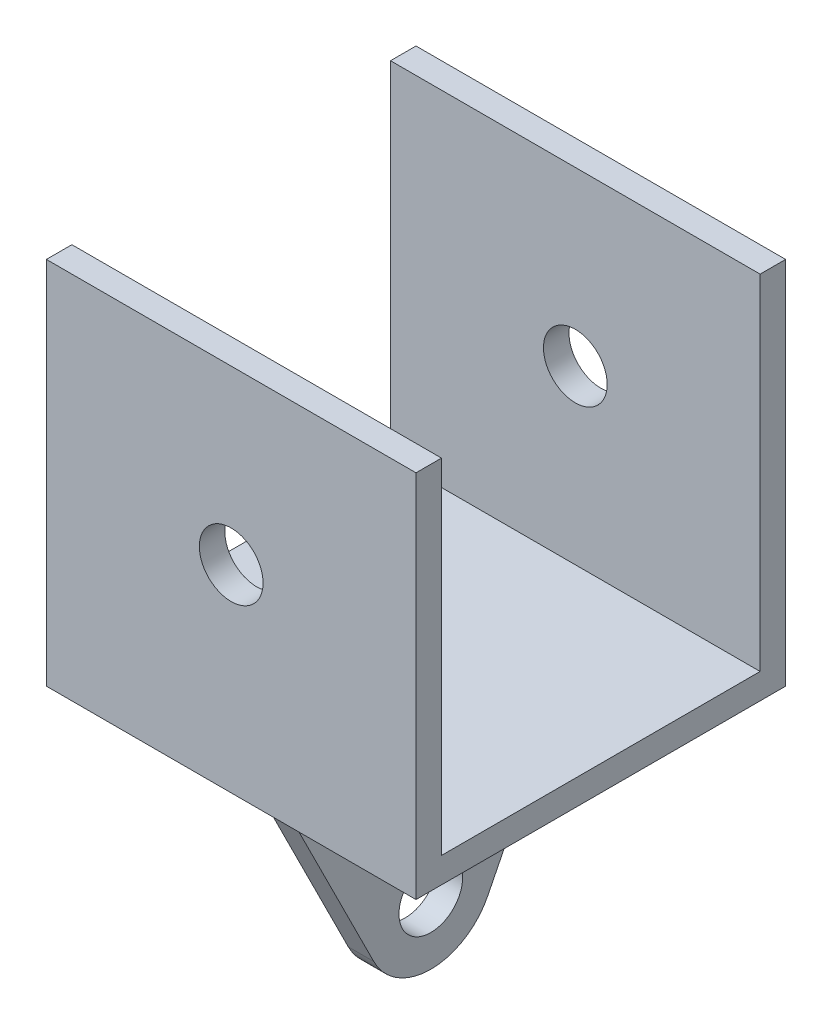
SolidWorks part; units mm, degrees
ref_plane "Front Plane" through (0, 0, 0) normal (0, 0, 1) x (1, 0, 0)
ref_plane "Top Plane" through (0, 0, 0) normal (0, 1, 0) x (1, 0, 0)
ref_plane "Right Plane" through (0, 0, 0) normal (1, 0, 0) x (0, 0, -1)
sketch "Sketch1" plane through (0, 0, 0) normal (0, 1, 0) x (1, 0, 0)
  line L0 (-14.5, 14.5) -> (14.5, -14.5) construction
  line L1 (-14.5, 14.5) -> (14.5, 14.5)
  line L2 (-14.5, 14.5) -> (-14.5, -14.5)
  line L3 (-14.5, -14.5) -> (14.5, -14.5)
  line L4 (14.5, 14.5) -> (14.5, -14.5)
extrude "Boss-Extrude1" add sketch "Sketch1" along normal blind 2
sketch "Sketch2" plane through (0, 2, 0) normal (0, 1, 0) x (1, 0, 0)
  line L0 (14.5, -14.5) -> (14.5, 14.5) construction
  line L1 (-14.5, -14.5) -> (14.5, -14.5)
  line L2 (-14.5, -14.5) -> (-14.5, -12.5)
  line L3 (-14.5, -12.5) -> (14.5, -12.5)
  line L4 (14.5, -14.5) -> (14.5, -12.5)
  dimension "D1" = 2
extrude "Boss-Extrude2" add sketch "Sketch2" along normal blind 27
mirror "Mirror1" about plane through (0, 0, 0) normal (0, 0, 1) of "Boss-Extrude2"
sketch "Sketch4" plane through (0, 0, 14.5) normal (0, 0, 1) x (1, 0, 0)
  line L0 (-14.5, 29) -> (14.5, 2) construction
  line L1 (14.5, 29) -> (14.5, 0) construction
  line L2 (-14.5, 0) -> (14.5, 0) construction
  line L3 (-14.5, 2) -> (14.5, 29) construction
  circle A0 centre (0, 15.5) radius 2.5
  dimension "D1" = 2
extrude "Cut-Extrude1" cut sketch "Sketch4" against normal through all
sketch "Sketch6" plane through (0, 0, 0) normal (1, 0, 0) x (0, 0, -1)
  line L0 (-12.3405, 0) -> (12.6624, 0)
  line L1 (-14.5, 0) -> (14.5, 0) construction
  line L2 (12.6624, 0) -> (4.633, -16.057)
  line L3 (-4.3111, -16.057) -> (-12.3405, 0)
  arc A0 (4.633, -16.057) -> (-4.3111, -16.057) centre (0.161, -13.8207) cw
  circle A1 centre (0.161, -13.8207) radius 2.5
  point P8 (0.161, -25)
  dimension "D2" = 5
  dimension "D1" = 25
extrude "Boss-Extrude3" add sketch "Sketch6" along normal blind 1 and the other way blind 1
